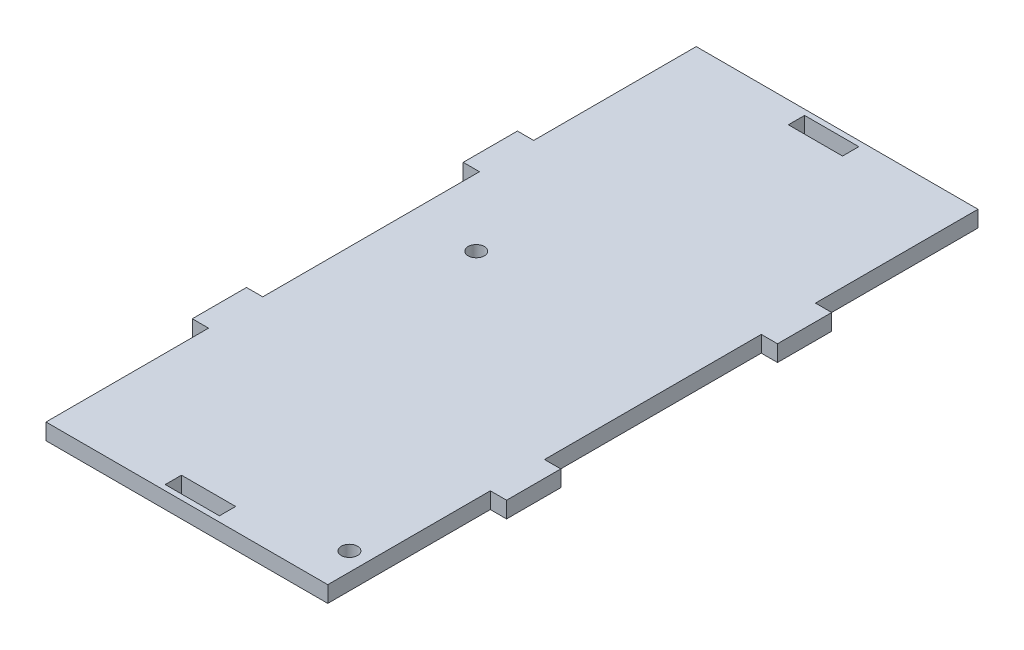
SolidWorks part; units mm, degrees
ref_plane "Front Plane" through (0, 0, 0) normal (0, 0, 1) x (1, 0, 0)
ref_plane "Top Plane" through (0, 0, 0) normal (0, 1, 0) x (1, 0, 0)
ref_plane "Right Plane" through (0, 0, 0) normal (1, 0, 0) x (0, 0, -1)
sketch "Sketch1" plane through (0, 0, 0) normal (0, 1, 0) x (1, 0, 0)
  line L0 (0, -42.4931) -> (0, 42.4931) construction
  line L1 (-5, -59) -> (5, -59)
  line L2 (-26, -30) -> (-26, -60)
  line L3 (-5, 56) -> (5, 59) construction
  line L4 (5, 59) -> (-5, 59)
  line L5 (26, -30) -> (26, -60)
  line L6 (26, 60) -> (26, 30)
  line L7 (26, 20) -> (29, 30) construction
  line L8 (-26, 30) -> (-29, 30)
  line L9 (-26, -20) -> (-26, 20)
  line L10 (26, 30) -> (29, 20) construction
  line L11 (-26, 20) -> (-29, 20)
  line L12 (-29, 30) -> (-29, 20)
  line L13 (0, 0) -> (93.5777, 0) construction
  line L14 (-26, 30) -> (-29, 20) construction
  line L15 (-26, 20) -> (-29, 30) construction
  line L16 (29, 30) -> (29, 20)
  line L17 (26, 20) -> (29, 20)
  line L18 (26, -20) -> (26, 20)
  line L19 (26, 30) -> (29, 30)
  line L20 (-26, -20) -> (-29, -30) construction
  line L21 (-26, -30) -> (-29, -20) construction
  line L22 (26, -30) -> (29, -20) construction
  line L23 (26, -20) -> (29, -30) construction
  line L24 (26, -30) -> (29, -30)
  line L25 (-5, 59) -> (5, 56) construction
  line L26 (26, -20) -> (29, -20)
  line L27 (29, -30) -> (29, -20)
  line L28 (-29, -30) -> (-29, -20)
  line L29 (-26, -20) -> (-29, -20)
  line L30 (-26, 60) -> (-26, 30)
  line L31 (-26, -30) -> (-29, -30)
  line L34 (5, 59) -> (5, 56)
  line L35 (-5, 56) -> (5, 56)
  line L36 (-5, 59) -> (-5, 56)
  line L40 (-26, -60) -> (26, -60)
  line L42 (-26, 60) -> (26, 60)
  line L44 (-26, -60) -> (26, 60) construction
  line L45 (-26, 60) -> (26, -60) construction
  line L46 (-5, -59) -> (-5, -56)
  line L47 (-5, -56) -> (5, -56)
  line L48 (5, -59) -> (5, -56)
  line L49 (-5, -59) -> (5, -56) construction
  line L50 (-5, -56) -> (5, -59) construction
  circle A0 centre (22.6, -52.6) radius 1.5 construction
  circle A1 centre (-13.6, 7) radius 1.5 construction
  circle A2 centre (22.6, -52.6) radius 1.5
  circle A3 centre (-13.6, 7) radius 1.5
  point P0 (0, 0)
  point P1 (0, 0)
  point P2 (0, 0)
  point P3 (0, 0)
  point P4 (0, 0)
  point P15 (-27.5, 25)
  point P20 (27.5, 25)
  point P29 (27.5, -25)
  point P34 (0, 57.5)
  point P35 (5, -57.5)
  point P44 (0, -57.5)
  point P47 (-27.5, -25)
  point P51 (0, 0)
  point P52 (0, 0)
  point P53 (-26, 0)
  point P54 (26, 0)
  point P55 (0, 0)
  point P56 (0, 0)
  dimension "D6" = 120
  dimension "D7" = 52
  dimension "D1" = 1.5
  dimension "D2" = 30
  dimension "D3" = 3
  dimension "D4" = 10
  dimension "D5" = 2.5
  dimension "D8" = 3
  dimension "D9" = 10
extrude "Boss-Extrude1" add sketch "Sketch1" along normal blind 3
